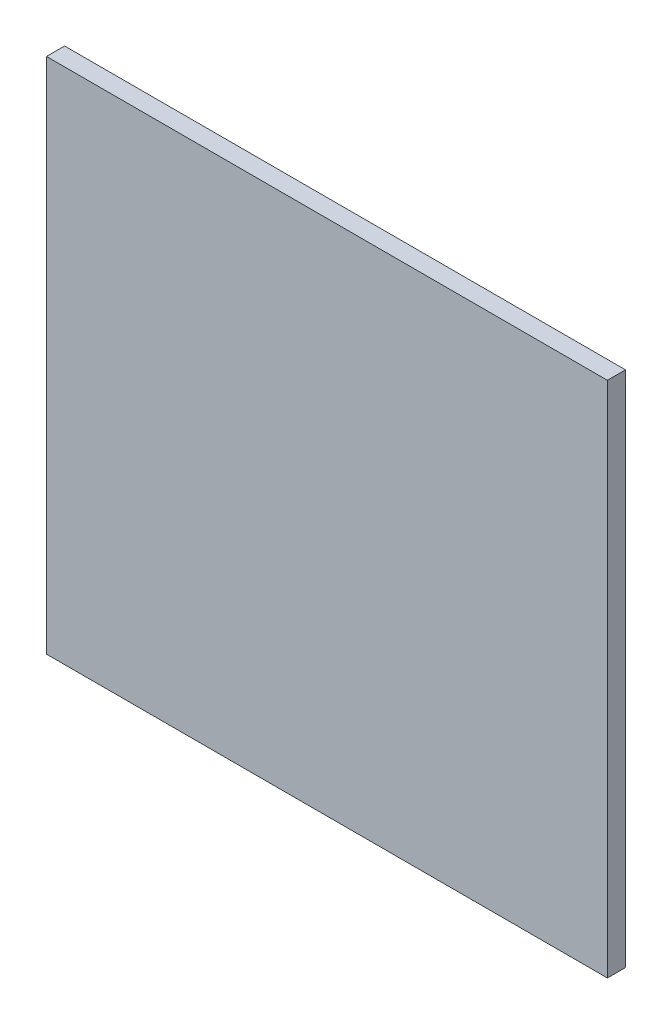
SolidWorks part; units mm, degrees
ref_plane "Front Plane" through (0, 0, 0) normal (0, 0, 1) x (1, 0, 0)
ref_plane "Top Plane" through (0, 0, 0) normal (0, 1, 0) x (1, 0, 0)
ref_plane "Right Plane" through (0, 0, 0) normal (1, 0, 0) x (0, 0, -1)
sketch "Sketch1" plane through (0, 0, 0) normal (0, 0, 1) x (1, 0, 0)
  line L1 (64.3464, -470.3515) -> (-493.6536, -470.3515)
  line L2 (64.3464, -470.3515) -> (64.3464, 44.6485)
  line L3 (64.3464, 44.6485) -> (-493.6536, 44.6485)
  line L4 (-493.6536, -470.3515) -> (-493.6536, 44.6485)
  line L5 (64.3464, -470.3515) -> (-493.6536, 44.6485) construction
  line L6 (64.3464, 44.6485) -> (-493.6536, -470.3515) construction
  point P0 (-214.6536, -212.8515)
  dimension "D1" = 558
  dimension "D2" = 515
extrude "Boss-Extrude1" add sketch "Sketch1" along normal blind 18
